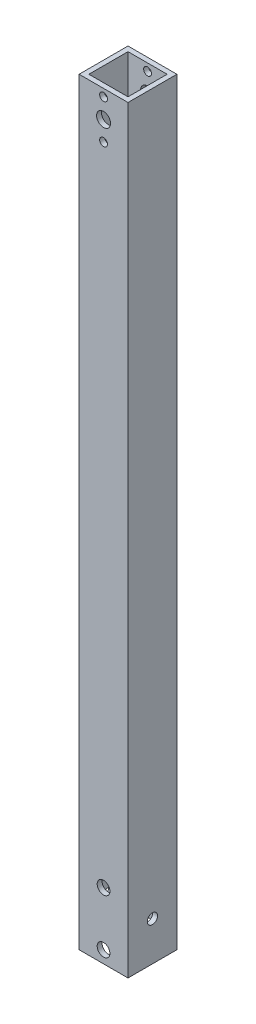
SolidWorks part; units mm, degrees
material "Gerais  - 6061-T6"
ref_plane "Plano frontal" through (0, 0, 0) normal (0, 0, 1) x (1, 0, 0)
ref_plane "Plano superior" through (0, 0, 0) normal (0, 1, 0) x (1, 0, 0)
ref_plane "Plano direito" through (0, 0, 0) normal (1, 0, 0) x (0, 0, -1)
sketch "Esboço1" plane through (0, 0, 0) normal (0, 1, 0) x (1, 0, 0)
  line L1 (0, 0) -> (20, 0)
  line L2 (0, 0) -> (0, 20)
  line L3 (0, 20) -> (20, 20)
  line L4 (20, 0) -> (20, 20)
  dimension "D1" = 20
extrude "Extrusão-Fina1" add sketch "Esboço1" along normal blind 310 thin thin type one direction reverse wall 2
sketch "Esboço4" plane through (0, 0, 0) normal (0, 0, 1) x (1, 0, 0)
  line L0 (10, 307) -> (10, 291) construction
  line L1 (0, 310) -> (20, 310) construction
  circle A0 centre (10, 299) radius 2.85
  circle A1 centre (10, 291) radius 1.6
  circle A2 centre (10, 307) radius 1.6
  circle A3 centre (10, 299) radius 11 construction
  point P8 (10, 310)
  dimension "D1" = 3.2
  dimension "D2" = 5.7
  dimension "D4" = 22
  dimension "D3" = 16
extrude "Corte-extrusão2" cut sketch "Esboço4" against normal through all
sketch "Esboço5" plane through (0, 0, -20) normal (0, 0, -1) x (-1, 0, 0)
  circle A2 centre (-10, 5) radius 2.6
  circle A3 centre (-10, 27) radius 2.6
extrude "Corte-extrusão5" cut sketch "Esboço5" against normal through all
sketch "Esboço6" plane through (0, 0, 0) normal (-1, 0, 0) x (0, 0, 1)
  line L0 (-20, 0) -> (0, 0) construction
  circle A0 centre (-10, 16) radius 2.1
  point P4 (-10, 0)
  dimension "D1" = 4.2
  dimension "D2" = 16
extrude "Corte-extrusão6" cut sketch "Esboço6" against normal through all
